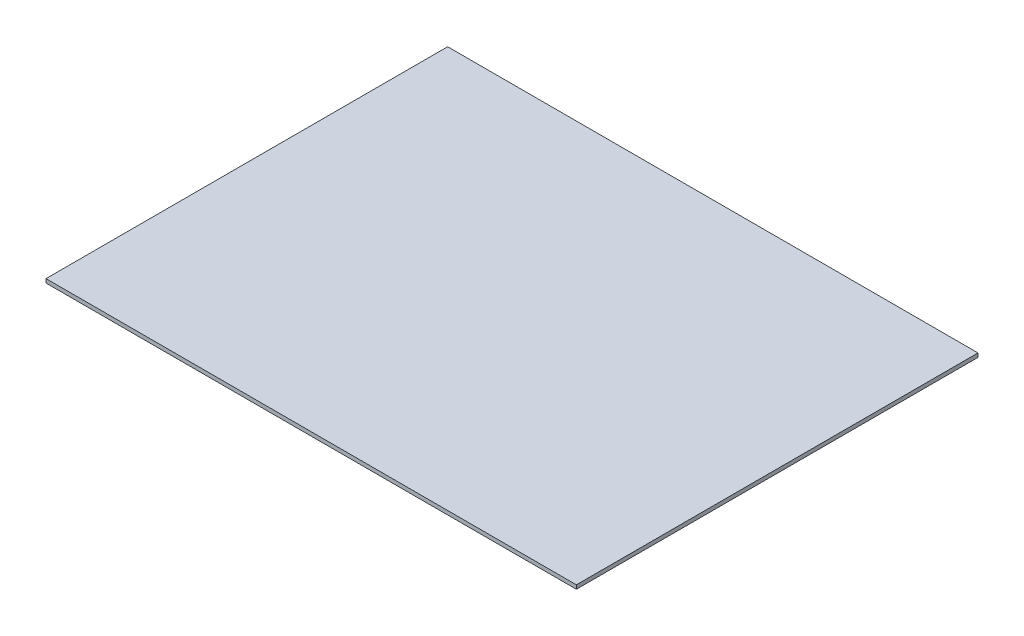
SolidWorks part; units mm, degrees
ref_plane "Front Plane" through (0, 0, 0) normal (0, 0, 1) x (1, 0, 0)
ref_plane "Top Plane" through (0, 0, 0) normal (0, 1, 0) x (1, 0, 0)
ref_plane "Right Plane" through (0, 0, 0) normal (1, 0, 0) x (0, 0, -1)
sketch "Sketch1" plane through (0, 0, 0) normal (0, 1, 0) x (1, 0, 0)
  line L0 (365.9882, 160.7571) -> (365.9882, -151.2429) construction
  line L5 (-46.0118, -151.2429) -> (365.9882, -151.2429) construction
  line L6 (-46.0118, 160.7571) -> (365.9882, 160.7571) construction
  line L7 (-46.0118, 160.7571) -> (-46.0118, -151.2429) construction
  line L8 (365.9882, 160.7571) -> (365.9882, -151.2429)
  line L9 (-46.0118, -151.2429) -> (365.9882, -151.2429)
  line L10 (-46.0118, 160.7571) -> (365.9882, 160.7571)
  line L11 (-46.0118, 160.7571) -> (-46.0118, -151.2429)
extrude "Boss-Extrude1" add sketch "Sketch1" along normal blind 3
